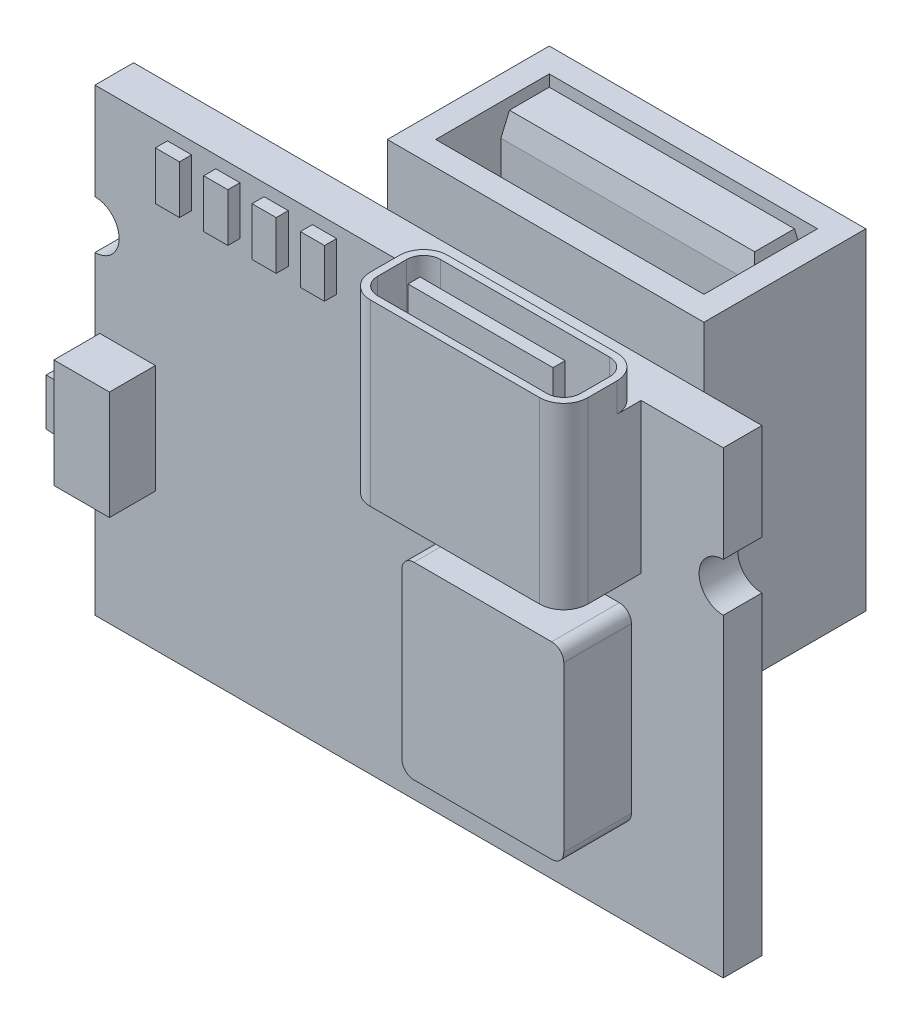
SolidWorks part; units mm, degrees
ref_plane "Plano frontal" through (0, 0, 0) normal (0, 0, 1) x (1, 0, 0)
ref_plane "Plano superior" through (0, 0, 0) normal (0, 1, 0) x (1, 0, 0)
ref_plane "Plano direito" through (0, 0, 0) normal (1, 0, 0) x (0, 0, -1)
sketch "Esboço1" plane through (0, 0, 0) normal (0, 0, 1) x (1, 0, 0)
  line L1 (-31.345, 15.4853) -> (-5.345, 15.4853)
  line L2 (-31.345, 15.4853) -> (-31.345, -3.5147)
  line L3 (-31.345, -3.5147) -> (-5.345, -3.5147)
  line L4 (-5.345, 15.4853) -> (-5.345, -3.5147)
  dimension "D1" = 26
  dimension "D2" = 19
extrude "Ressalto-extrusão1" add sketch "Esboço1" along normal blind 1.6
sketch "Esboço2" plane through (0, 0, 1.6) normal (0, 0, 1) x (1, 0, 0)
  line L0 (-31.345, 15.4853) -> (-31.345, -3.5147) construction
  line L13 (-28.345, 14.9853) -> (-27.345, 14.9853)
  line L14 (-28.345, 14.9853) -> (-28.345, 12.9853)
  line L15 (-28.345, 12.9853) -> (-27.345, 12.9853)
  line L16 (-27.345, 14.9853) -> (-27.345, 12.9853)
  line L17 (-26.345, 14.9853) -> (-25.345, 14.9853)
  line L18 (-26.345, 14.9853) -> (-26.345, 12.9853)
  line L19 (-26.345, 12.9853) -> (-25.345, 12.9853)
  line L20 (-25.345, 14.9853) -> (-25.345, 12.9853)
  line L21 (-24.345, 14.9853) -> (-23.345, 14.9853)
  line L22 (-24.345, 14.9853) -> (-24.345, 12.9853)
  line L23 (-24.345, 12.9853) -> (-23.345, 12.9853)
  line L24 (-23.345, 14.9853) -> (-23.345, 12.9853)
  line L25 (-22.345, 14.9853) -> (-21.345, 14.9853)
  line L26 (-22.345, 14.9853) -> (-22.345, 12.9853)
  line L27 (-22.345, 12.9853) -> (-21.345, 12.9853)
  line L28 (-21.345, 14.9853) -> (-21.345, 12.9853)
  line L29 (-5.345, 15.4853) -> (-31.345, 15.4853) construction
  dimension "D1" = 2
  dimension "D2" = 1
  dimension "D3" = 3
  dimension "D4" = 1
  dimension "D5" = 1
  dimension "D6" = 1
  dimension "D7" = 0.5
extrude "Ressalto-extrusão2" add sketch "Esboço2" along normal blind 0.5
sketch "Esboço3" plane through (0, 0, 1.6) normal (0, 0, 1) x (1, 0, 0)
  line L0 (-5.345, 15.4853) -> (-31.345, 15.4853) construction
  line L1 (-17.745, 16.6853) -> (-8.745, 16.6853)
  line L2 (-17.745, 16.6853) -> (-17.745, 9.2853)
  line L3 (-17.745, 9.2853) -> (-8.745, 9.2853)
  line L4 (-8.745, 16.6853) -> (-8.745, 9.2853)
  line L5 (-5.345, -3.5147) -> (-5.345, 15.4853) construction
  dimension "D1" = 9
  dimension "D2" = 7.4
  dimension "D3" = 1.2
  dimension "D4" = 3.4
extrude "Ressalto-extrusão3" add sketch "Esboço3" along normal blind 3.2
fillet "Filete1" radius 1 1 edges at (-8.745, 12.9853, 4.8)
fillet "Filete7" radius 1 3 edges at (-17.745, 16.0853, 1.6) (-8.745, 16.0853, 1.6) (-17.745, 12.9853, 4.8)
sketch "Esboço4" plane through (0, 16.6853, 0) normal (0, 1, 0) x (1, 0, 0)
  line L8 (-9.745, -1.9) -> (-16.745, -1.9)
  line L9 (-17.445, -2.6) -> (-17.445, -3.8)
  line L10 (-16.745, -4.5) -> (-9.745, -4.5)
  line L11 (-9.045, -3.8) -> (-9.045, -2.6)
  line L12 (-9.745, -1.9) -> (-16.745, -1.9)
  line L13 (-17.445, -2.6) -> (-17.445, -3.8)
  line L14 (-16.745, -4.5) -> (-9.745, -4.5)
  line L15 (-9.045, -3.8) -> (-9.045, -2.6)
  arc A8 (-16.745, -1.9) -> (-17.445, -2.6) centre (-16.745, -2.6) ccw
  arc A9 (-17.445, -3.8) -> (-16.745, -4.5) centre (-16.745, -3.8) ccw
  arc A10 (-9.745, -4.5) -> (-9.045, -3.8) centre (-9.745, -3.8) ccw
  arc A11 (-9.045, -2.6) -> (-9.745, -1.9) centre (-9.745, -2.6) ccw
  arc A12 (-16.745, -1.9) -> (-17.445, -2.6) centre (-16.745, -2.6) ccw
  arc A13 (-17.445, -3.8) -> (-16.745, -4.5) centre (-16.745, -3.8) ccw
  arc A14 (-9.745, -4.5) -> (-9.045, -3.8) centre (-9.745, -3.8) ccw
  arc A15 (-9.045, -2.6) -> (-9.745, -1.9) centre (-9.745, -2.6) ccw
  dimension "D1" = 0.3
extrude "Corte-extrusão1" cut sketch "Esboço4" against normal blind 5.2
sketch "Esboço5" plane through (0, 16.6853, 0) normal (0, 1, 0) x (1, 0, 0)
  line L1 (-10.5396, -3.45) -> (-16.5396, -3.45)
  line L2 (-10.5396, -3.45) -> (-10.5396, -2.95)
  line L3 (-10.5396, -2.95) -> (-16.5396, -2.95)
  line L4 (-16.5396, -3.45) -> (-16.5396, -2.95)
  line L5 (-9.745, -1.9) -> (-16.745, -1.9) construction
  dimension "D1" = 6
  dimension "D2" = 0.5
  dimension "D3" = 1.05
extrude "Ressalto-extrusão4" add sketch "Esboço5" against normal up to next
sketch "Esboço6" plane through (0, 0, 1.6) normal (0, 0, 1) x (1, 0, 0)
  line L0 (-5.345, -3.5147) -> (-5.345, 15.4853) construction
  line L1 (-15.845, 7.7853) -> (-9.145, 7.7853)
  line L2 (-15.845, 7.7853) -> (-15.845, -0.0147)
  line L3 (-15.845, -0.0147) -> (-9.145, -0.0147)
  line L4 (-9.145, 7.7853) -> (-9.145, -0.0147)
  line L5 (-31.345, -3.5147) -> (-5.345, -3.5147) construction
  dimension "D1" = 6.7
  dimension "D2" = 7.8
  dimension "D3" = 3.8
  dimension "D4" = 3.5
extrude "Ressalto-extrusão5" add sketch "Esboço6" along normal blind 2.8
fillet "Filete8" radius 0.5 4 edges at (-9.145, 7.7853, 3) (-15.845, 7.7853, 3) (-15.845, -0.0147, 3) (-9.145, -0.0147, 3)
sketch "Esboço7" plane through (0, 0, 1.6) normal (0, 0, 1) x (1, 0, 0)
  line L0 (-31.345, 15.4853) -> (-31.345, -3.5147) construction
  line L1 (-31.145, 6.6853) -> (-28.845, 6.6853)
  line L2 (-31.145, 6.6853) -> (-31.145, 2.1853)
  line L3 (-31.145, 2.1853) -> (-28.845, 2.1853)
  line L4 (-28.845, 6.6853) -> (-28.845, 2.1853)
  line L5 (-31.345, -3.5147) -> (-5.345, -3.5147) construction
  dimension "D1" = 4.5
  dimension "D2" = 2.3
  dimension "D3" = 0.2
  dimension "D4" = 5.7
extrude "Ressalto-extrusão6" add sketch "Esboço7" along normal blind 1.9
sketch "Esboço8" plane through (-31.145, 0, 0) normal (-1, 0, 0) x (0, 0, 1)
  line L1 (2.95, 5.4353) -> (2.15, 5.4353)
  line L2 (2.95, 5.4353) -> (2.95, 3.4353)
  line L3 (2.95, 3.4353) -> (2.15, 3.4353)
  line L4 (2.15, 5.4353) -> (2.15, 3.4353)
  line L5 (3.5, 6.6853) -> (3.5, 2.1853) construction
  line L7 (3.5, 6.6853) -> (1.6, 6.6853) construction
  dimension "D1" = 2
  dimension "D2" = 0.8
  dimension "D3" = 0.55
  dimension "D4" = 1.25
extrude "Ressalto-extrusão7" add sketch "Esboço8" along normal blind 0.9 draft 2
sketch "Esboço9" plane through (0, 0, 0) normal (0, 0, -1) x (-1, 0, 0)
  line L0 (31.345, -3.5147) -> (5.345, -3.5147) construction
  line L1 (22.145, 2.9853) -> (9.045, 2.9853)
  line L2 (22.145, 2.9853) -> (22.145, 16.6853)
  line L3 (22.145, 16.6853) -> (9.045, 16.6853)
  line L4 (9.045, 2.9853) -> (9.045, 16.6853)
  line L5 (5.345, -3.5147) -> (5.345, 15.4853) construction
  dimension "D1" = 13.1
  dimension "D2" = 13.7
  dimension "D3" = 6.5
  dimension "D4" = 3.7
extrude "Ressalto-extrusão8" add sketch "Esboço9" along normal blind 8
sketch "Esboço10" plane through (0, 16.6853, 0) normal (0, 1, 0) x (1, 0, 0)
  line L0 (-22.145, 8) -> (-9.045, 8) construction
  line L1 (-22.145, 1.3) -> (-9.045, 1.3)
  line L2 (-22.145, 1.3) -> (-22.145, 0)
  line L3 (-22.145, 0) -> (-9.045, 0)
  line L4 (-9.045, 1.3) -> (-9.045, 0)
  line L6 (-22.145, 8) -> (-22.145, 0) construction
  line L7 (-9.045, 8) -> (-9.045, 0) construction
  line L9 (-22.145, 0) -> (-9.045, 0) construction
  dimension "D1" = 6.7
extrude "Corte-extrusão2" cut sketch "Esboço10" against normal blind 9
sketch "Esboço11" plane through (0, 16.6853, 0) normal (0, 1, 0) x (1, 0, 0)
  line L0 (-9.045, 1.3) -> (-22.145, 1.3) construction
  line L1 (-21.145, 7) -> (-10.045, 7)
  line L2 (-21.145, 7) -> (-21.145, 2.3)
  line L3 (-21.145, 2.3) -> (-10.045, 2.3)
  line L4 (-10.045, 7) -> (-10.045, 2.3)
  line L5 (-9.045, 8) -> (-9.045, 1.3) construction
  line L6 (-22.145, 8) -> (-22.145, 1.3) construction
  line L7 (-22.145, 8) -> (-9.045, 8) construction
  dimension "D1" = 1
  dimension "D2" = 1
  dimension "D3" = 1
  dimension "D4" = 1
extrude "Corte-extrusão3" cut sketch "Esboço11" against normal blind 9
sketch "Esboço12" plane through (0, 16.6853, 0) normal (0, 1, 0) x (1, 0, 0)
  line L0 (-21.145, 2.3) -> (-10.045, 2.3) construction
  line L1 (-20.845, 6.7) -> (-10.345, 6.7)
  line L2 (-20.845, 6.7) -> (-20.845, 4.7)
  line L3 (-20.845, 4.7) -> (-10.345, 4.7)
  line L4 (-10.345, 6.7) -> (-10.345, 4.7)
  line L5 (-10.045, 2.3) -> (-10.045, 7) construction
  line L6 (-21.145, 7) -> (-21.145, 2.3) construction
  dimension "D1" = 2.4
  dimension "D2" = 0.3
  dimension "D3" = 0.3
  dimension "D4" = 2
extrude "Ressalto-extrusão9" add sketch "Esboço12" against normal up to next
chamfer "Chanfro1" distance 1 angle 10 4 edges at (-15.595, 16.6853, -6.7) (-10.345, 16.6853, -5.7) (-15.595, 16.6853, -4.7) (-20.845, 16.6853, -5.7)
sketch "Esboço13" plane through (0, 0, 1.6) normal (0, 0, 1) x (1, 0, 0)
  line L0 (-17.745, 15.4853) -> (-31.345, 15.4853) construction
  line L1 (-31.345, 15.4853) -> (-31.345, -3.5147) construction
  line L2 (-18.345, -3.5147) -> (-18.345, 15.4853) construction
  line L3 (-31.345, -3.5147) -> (-5.345, -3.5147) construction
  circle A0 centre (-31.345, 10.4853) radius 1
  circle A1 centre (-5.345, 10.4853) radius 1
  dimension "D2" = 2
  dimension "D1" = 5
  dimension "D3" = 0
extrude "Corte-extrusão4" cut sketch "Esboço13" against normal up to next
